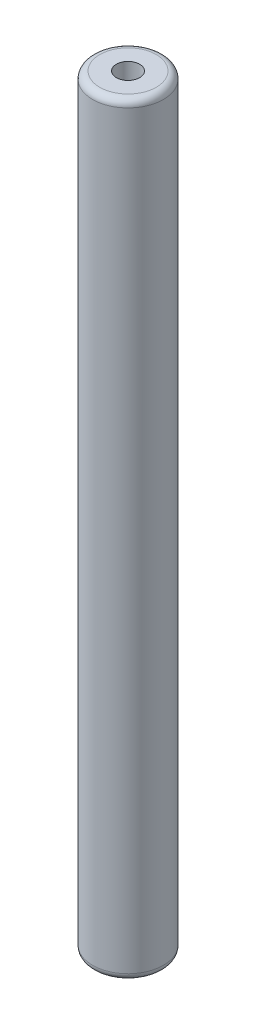
SolidWorks part; units mm, degrees
material "Alumina"
ref_plane "Front Plane" through (0, 0, 0) normal (0, 0, 1) x (1, 0, 0)
ref_plane "Top Plane" through (0, 0, 0) normal (0, 1, 0) x (1, 0, 0)
ref_plane "Right Plane" through (0, 0, 0) normal (1, 0, 0) x (0, 0, -1)
sketch "Sketch1" plane through (0, 0, 0) normal (0, 1, 0) x (1, 0, 0)
  circle A0 centre (0, 0) radius 2.5
  dimension "D1" = 5
extrude "Boss-Extrude1" add sketch "Sketch1" along normal blind 27
sketch "Sketch2" plane through (0, 27, 0) normal (0, 1, 0) x (1, 0, 0)
  circle A0 centre (0, 0) radius 0.825
  dimension "D1" = 1.65
extrude "Cut-Extrude1" cut sketch "Sketch2" against normal blind 5
sketch "Sketch3" plane through (0, 27, 0) normal (0, 1, 0) x (1, 0, 0)
  line L0 (2, 1.5) -> (2, -1.5)
  circle A0 centre (0, 0) radius 2.5 construction
  arc A1 (2, -1.5) -> (2, 1.5) centre (0, 0) ccw
  dimension "D1" = 3
extrude "Cut-Extrude2" [suppressed] cut sketch "Sketch3" against normal through all
fillet "Fillet1" radius 0.5 1 edges at (0, 27, 2.5)
mirror "Mirror1" about plane through (0, 0, 0) normal (0, 1, 0) of "Fillet1", "Cut-Extrude2", "Cut-Extrude1", "Boss-Extrude1"
